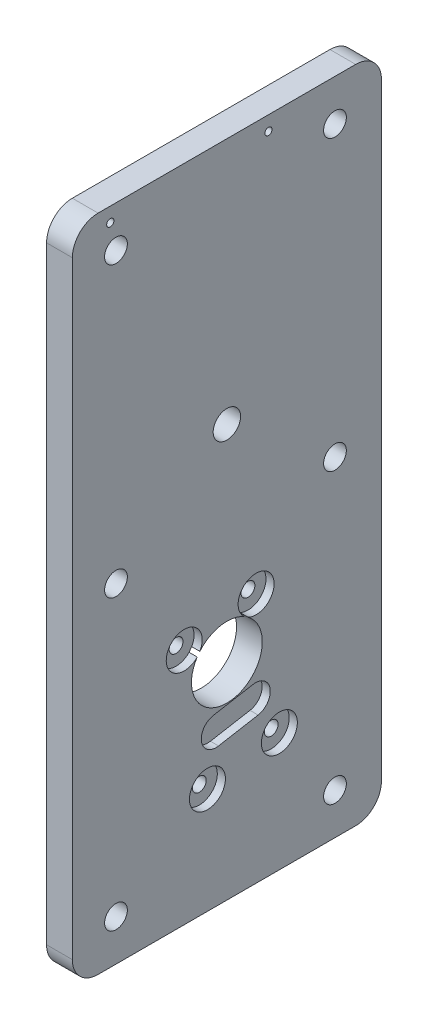
SolidWorks part; units mm, degrees
ref_plane "Front Plane" through (0, 0, 0) normal (0, 0, 1) x (1, 0, 0)
ref_plane "Top Plane" through (0, 0, 0) normal (0, 1, 0) x (1, 0, 0)
ref_plane "Right Plane" through (0, 0, 0) normal (1, 0, 0) x (0, 0, -1)
sketch "Sketch1" plane through (0, 0, 0) normal (1, 0, 0) x (0, 0, -1)
  line L15 (34.2822, -22.4869) -> (34.2822, 133.7231)
  line L16 (34.2822, 133.7231) -> (-41.9178, 133.7231)
  line L17 (-41.9178, 133.7231) -> (-41.9178, -22.4869)
  line L18 (-35.5678, -28.8369) -> (27.9322, -28.8369)
  arc A0 (-10.6087, -12.2953) -> (28.4055, 35.4321) centre (-3.8178, 21.9631) ccw construction
  arc A2 (28.4055, 35.4321) -> (-36.0411, 35.4321) centre (-3.8178, 21.9631) ccw construction
  circle A5 centre (-3.8178, 21.9631) radius 8.7312
  arc A6 (-36.0411, 35.4321) -> (-10.6087, -12.2953) centre (-3.8178, 21.9631) ccw construction
  arc A11 (34.2822, -22.4869) -> (27.9322, -28.8369) centre (27.9322, -22.4869) cw
  arc A15 (-41.9178, -22.4869) -> (-35.5678, -28.8369) centre (-35.5678, -22.4869) ccw
  circle A18 centre (-3.8178, 21.9631) radius 9.525 construction
  point P9 (34.2822, -28.8369)
  point P14 (-41.9178, -28.8369)
  point P22 (-41.9178, 133.7231)
  point P27 (-41.9178, 133.7231)
  dimension "D1" = 34.925
  dimension "D2" = 6.35
  dimension "D4" = 38.1
  dimension "D5" = 17.4625
  dimension "D6" = 76.2
  dimension "D7" = 162.56
  dimension "D8" = 19.05
  dimension "D3" = 50.8
extrude "Boss-Extrude1" add sketch "Sketch1" along normal blind 6.35
sketch "Sketch7" plane through (6.35, 0, 0) normal (1, 0, 0) x (0, 0, -1)
  line L0 (-7.0256, 11.6494) -> (2.724, 13.3685) construction
  line L1 (3.7659, 7.4596) -> (-5.9837, 5.7405) construction
  line L2 (-7.0256, 11.6494) -> (2.724, 13.3685) construction
  line L3 (3.7659, 7.4596) -> (-5.9837, 5.7405) construction
  line L4 (-7.1358, 12.2747) -> (2.6138, 13.9938)
  line L5 (3.8762, 6.8343) -> (-5.8734, 5.1152)
  circle A0 centre (-3.8178, 21.9631) radius 6.6 construction
  circle A1 centre (3.389, 32.9204) radius 3.8 construction
  circle A2 centre (-14.3376, 29.7947) radius 3.8 construction
  arc A3 (-7.0256, 11.6494) -> (-5.9837, 5.7405) centre (-6.5046, 8.6949) ccw construction
  arc A4 (3.7659, 7.4596) -> (2.724, 13.3685) centre (3.245, 10.4141) ccw construction
  circle A5 centre (9.1194, 0.4217) radius 3.8 construction
  circle A6 centre (-8.6072, -2.704) radius 3.8 construction
  circle A7 centre (-3.8178, 21.9631) radius 6.6 construction
  circle A8 centre (3.389, 32.9204) radius 3.8 construction
  circle A9 centre (-14.3376, 29.7947) radius 3.8 construction
  arc A10 (-7.0256, 11.6494) -> (-5.9837, 5.7405) centre (-6.5046, 8.6949) ccw construction
  arc A11 (3.7659, 7.4596) -> (2.724, 13.3685) centre (3.245, 10.4141) ccw construction
  circle A12 centre (9.1194, 0.4217) radius 3.8 construction
  circle A13 centre (-8.6072, -2.704) radius 3.8 construction
  arc A14 (3.8762, 6.8343) -> (2.6138, 13.9938) centre (3.245, 10.4141) ccw
  arc A15 (-7.1358, 12.2747) -> (-5.8734, 5.1152) centre (-6.5046, 8.6949) ccw
  circle A16 centre (-3.8178, 21.9631) radius 7.235
  circle A17 centre (3.389, 32.9204) radius 4.435
  circle A18 centre (-14.3376, 29.7947) radius 4.435
  circle A19 centre (9.1194, 0.4217) radius 4.435
  circle A20 centre (-8.6072, -2.704) radius 4.435
  dimension "D1" = 0.635
extrude "Cut-Extrude2" cut sketch "Sketch7" against normal blind 2
hole_wizard "M3 Clearance Hole2" positions "Sketch8" profile "Sketch9" hole size "M3" standard "ANSI Metric" end condition through all
sketch "Sketch8" plane through (6.35, 0, 0) normal (1, 0, 0) x (0, 0, -1)
  point P0 (9.1194, 0.4217)
  point P3 (-8.6072, -2.704)
  point P6 (-14.3376, 29.7947)
  point P9 (3.389, 32.9204)
sketch "Sketch9" plane through (6.35, 0.4217, -9.1194) normal (0, 1, 0) x (0, 0, -1)
  line L0 (0, 0) -> (0, 6.35)
  line L1 (0, 6.35) -> (1.7, 6.35)
  line L2 (1.7, 6.35) -> (1.7, 0)
  line L5 (1.7, 0) -> (0, 0)
  line L11 (0, -6.35) -> (0, 107.95) construction
  dimension "Thru Hole Dia." = 3.4
  dimension "Thru Hole Depth" = 6.35
hole_wizard "1/4 Clearance Hole1" positions "Sketch10" profile "Sketch11" hole size "1/4" standard "ANSI Inch"
sketch "Sketch10" plane through (6.35, 0, 0) normal (1, 0, 0) x (0, 0, -1)
  line L1 (-45.6973, -33.5192) -> (30.5027, -33.5192) construction
  line L2 (-32.9973, 156.9808) -> (17.8027, 156.9808) construction
  line L4 (-7.5973, 169.6808) -> (-7.5973, -33.5192) construction
  line L5 (30.5027, 169.6808) -> (-45.6973, 169.6808) construction
  line L6 (-32.9973, -20.8192) -> (17.8027, -20.8192) construction
  line L8 (-45.6973, 169.6808) -> (-45.6973, -33.5192) construction
  point P0 (-32.9973, -20.8192)
  point P3 (17.8027, -20.8192)
  point P6 (-7.5973, 106.1808)
  point P9 (-32.9973, 156.9808)
  point P11 (17.8027, 156.9808)
  point P25 (-7.5973, 156.9808)
  dimension "D1" = 190.5
  dimension "D2" = 12.7
  dimension "D3" = 139.7
  dimension "D5" = 12.7
  dimension "D6" = 50.8
sketch "Sketch11" plane through (6.35, -20.8192, 32.9973) normal (0, 1, 0) x (0, 0, -1)
  line L0 (0, 0) -> (0, 6.35)
  line L1 (0, 6.35) -> (3.3782, 6.35)
  line L2 (3.3782, 6.35) -> (3.3782, 0)
  line L5 (3.3782, 0) -> (0, 0)
  line L11 (0, -6.35) -> (0, 107.95) construction
  dimension "Thru Hole Dia." = 6.7564
  dimension "Thru Hole Depth" = 6.35
hole_wizard "#2 (0.221) Diameter Hole1" positions "Sketch14" profile "Sketch15" hole size "#2" standard "ANSI Inch" end condition up to next
sketch "Sketch14" plane through (0, 0, 0) normal (-1, 0, 0) x (0, 0, 1)
  point P0 (-22.8287, 123.5633)
  point P3 (31.1598, 123.5633)
  point P6 (31.1598, 52.4433)
  point P9 (-22.8287, 52.4433)
  point P12 (-22.8287, -18.6767)
  point P15 (31.1598, -18.6767)
sketch "Sketch15" plane through (0, 123.5633, -22.8287) normal (0, 1, 0) x (0, 0, 1)
  line L0 (0, 0) -> (0, 6.35)
  line L1 (0, 6.35) -> (2.8067, 6.35)
  line L2 (2.8067, 6.35) -> (2.8067, 0)
  line L5 (2.8067, 0) -> (0, 0)
  line L11 (0, -6.35) -> (0, 107.95) construction
  dimension "Thru Hole Dia." = 5.6134
  dimension "Thru Hole Depth" = 6.35
hole_wizard "1/4 Clearance Hole2" positions "Sketch16" profile "Sketch17" hole size "1/4" standard "ANSI Inch" end condition through all
sketch "Sketch16" plane through (6.35, 0, 0) normal (1, 0, 0) x (0, 0, -1)
  line L0 (-41.9178, 72.7631) -> (34.2822, 72.7631) construction
  line L1 (-41.9178, 133.7231) -> (-41.9178, -22.4869) construction
  line L2 (34.2822, -22.4869) -> (34.2822, 133.7231) construction
  line L4 (-3.8178, -28.8369) -> (-3.8178, 129.052) construction
  line L5 (-35.5678, -28.8369) -> (27.9322, -28.8369) construction
  point P0 (-3.8178, 72.7631)
  dimension "D1" = 101.6
sketch "Sketch17" plane through (6.35, 72.7631, 3.8178) normal (0, 1, 0) x (0, 0, -1)
  line L0 (0, 0) -> (0, 6.35)
  line L1 (0, 6.35) -> (3.3782, 6.35)
  line L2 (3.3782, 6.35) -> (3.3782, 0)
  line L5 (3.3782, 0) -> (0, 0)
  line L11 (0, -6.35) -> (0, 107.95) construction
  dimension "Thru Hole Dia." = 6.7564
  dimension "Thru Hole Depth" = 6.35
hole_wizard "Tap Drill for #2-56 Tap2" positions "Sketch20" profile "Sketch22" hole size "#2-56" standard "ANSI Inch"
sketch "Sketch20" plane through (0, 167.1408, -34.2822) normal (0, 0, -1) x (1, 0, 0)
  point P0 (3.175, 58.8175)
  point P3 (3.175, 79.1375)
sketch "Sketch22" plane through (3.175, 108.3233, -34.2822) normal (1, 0, 0) x (0, 1, 0)
  line L0 (0, 0) -> (0, 13.2342)
  line L1 (0, 13.2342) -> (0.889, 12.7)
  line L2 (0.889, 12.7) -> (0.889, 0)
  line L5 (0.889, 0) -> (0, 0)
  line L10 (0, 13.2342) -> (-0.889, 12.7) construction
  line L11 (0, -6.35) -> (0, 107.95) construction
  dimension "Hole Dia." = 1.778
  dimension "Hole Depth" = 12.7
  dimension "Drill Angle" = 118
fillet "Fillet1" radius 6.35 2 edges at (3.175, 133.7231, 41.9178) (3.175, 133.7231, -34.2822)
hole_wizard "Tap Drill for #2-56 Tap1" positions "Sketch18" profile "Sketch19" hole size "#2-56" standard "ANSI Inch" end condition through all
sketch "Sketch18" plane through (6.35, 0, 0) normal (1, 0, 0) x (0, 0, -1)
  point P0 (6.4322, 130.1579)
  point P3 (-32.5678, 130.1579)
sketch "Sketch19" plane through (6.35, 130.1579, -6.4322) normal (0, 1, 0) x (0, 0, -1)
  line L0 (0, 0) -> (0, 6.35)
  line L1 (0, 6.35) -> (0.889, 6.35)
  line L2 (0.889, 6.35) -> (0.889, 0)
  line L5 (0.889, 0) -> (0, 0)
  line L11 (0, -6.35) -> (0, 107.95) construction
  dimension "Thru Hole Dia." = 1.778
  dimension "Thru Hole Depth" = 6.35
